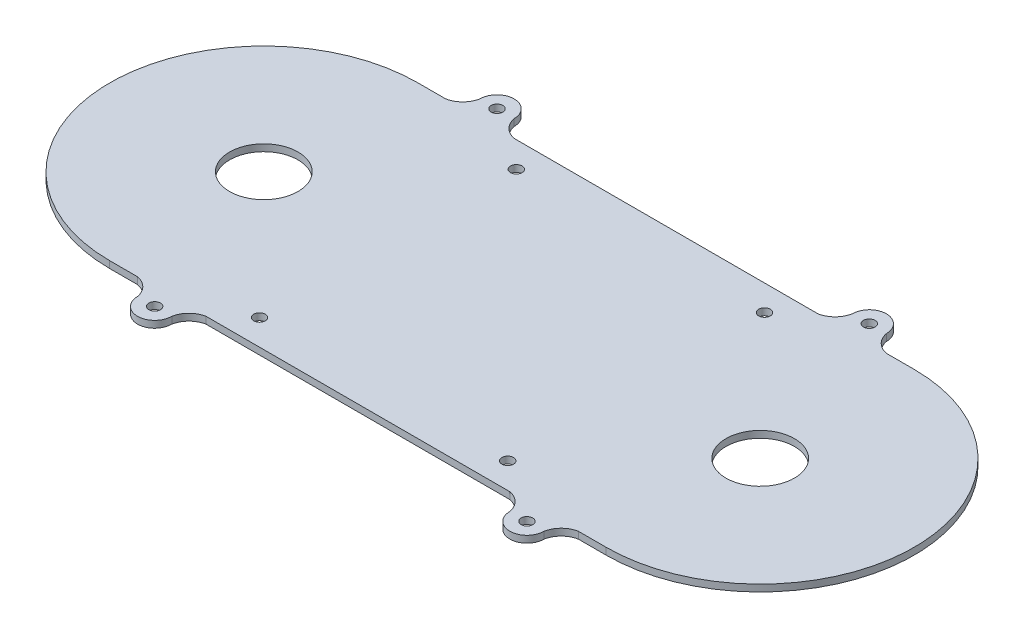
SolidWorks part; units mm, degrees
ref_plane "Front Plane" through (0, 0, 0) normal (0, 0, 1) x (1, 0, 0)
ref_plane "Top Plane" through (0, 0, 0) normal (0, 1, 0) x (1, 0, 0)
ref_plane "Right Plane" through (0, 0, 0) normal (1, 0, 0) x (0, 0, -1)
sketch "Sketch1" plane through (0, 0, 0) normal (0, 1, 0) x (1, 0, 0)
  line L0 (0, 45) -> (8.125, 45)
  line L1 (0, -45) -> (8.125, -45)
  line L2 (0, 0) -> (145, 0) construction
  line L3 (0, -45) -> (8.125, -45)
  line L4 (0, -45) -> (8.125, -45)
  line L6 (145, -45) -> (136.875, -45)
  line L8 (28.125, 45) -> (116.875, 45)
  line L9 (136.875, 45) -> (145, 45)
  line L10 (28.125, -45) -> (116.875, -45)
  line L11 (28.125, -45) -> (36.25, -45)
  line L12 (136.875, -45) -> (145, -45)
  arc A0 (0, 45) -> (0, -45) centre (0, 0) ccw
  arc A1 (145, -45) -> (145, 45) centre (145, 0) ccw
  arc A13 (13.125, -50) -> (23.125, -50) centre (18.125, -50) ccw
  arc A14 (13.125, -50) -> (8.125, -45) centre (6.9406, -51.1844) ccw
  arc A15 (23.125, -50) -> (28.125, -45) centre (29.3094, -51.1844) cw
  arc A16 (121.875, -50) -> (116.875, -45) centre (115.6906, -51.1844) ccw
  arc A17 (121.875, -50) -> (131.875, -50) centre (126.875, -50) ccw
  arc A18 (131.875, -50) -> (136.875, -45) centre (138.0594, -51.1844) cw
  arc A19 (131.875, 50) -> (136.875, 45) centre (138.0594, 51.1844) ccw
  arc A20 (121.875, 50) -> (131.875, 50) centre (126.875, 50) cw
  arc A21 (121.875, 50) -> (116.875, 45) centre (115.6906, 51.1844) cw
  arc A22 (23.125, 50) -> (28.125, 45) centre (29.3094, 51.1844) ccw
  arc A23 (13.125, 50) -> (23.125, 50) centre (18.125, 50) cw
  arc A24 (13.125, 50) -> (8.125, 45) centre (6.9406, 51.1844) cw
  circle A25 centre (108.75, -37.5) radius 1.7
  circle A26 centre (36.25, -37.5) radius 1.7
  circle A27 centre (36.25, 37.5) radius 1.7
  circle A28 centre (108.75, 37.5) radius 1.7
  dimension "D1" = 2
  dimension "D2" = 0
  dimension "D4" = 2
  dimension "D5" = 2
extrude "Boss-Extrude1" add sketch "Sketch1" along normal blind 2
sketch "Sketch2" plane through (0, 2, 0) normal (0, 1, 0) x (1, 0, 0)
  line L0 (0, 0) -> (126.8668, 0) construction
  circle A0 centre (18.1168, -49.9942) radius 5.01
  circle A1 centre (18.1168, -49.9942) radius 1.7
  circle A2 centre (126.8668, -49.9942) radius 1.7
  circle A3 centre (126.8668, 49.9942) radius 1.7
  circle A4 centre (18.1168, 49.9942) radius 1.7
  dimension "D1" = 2
extrude "Cut-Extrude1" cut sketch "Sketch2" against normal blind 4 contours A1 | A2 | A3 | A4
sketch "Sketch3" plane through (0, 0, 0) normal (0, -1, 0) x (-1, 0, 0)
  line L0 (0, 0) -> (-72.5, 0) construction
ref_plane "Plane1" through (72.5, 0, 0) normal (-1, 0, 0) x (0, 0, 1)
sketch "Sketch4" plane through (72.5, 0, 0) normal (-1, 0, 0) x (0, 0, 1)
  line L0 (0, 0) -> (5, 0)
  line L1 (-45, 0) -> (45, 0) construction
  line L2 (0, 0) -> (0, 2)
  line L3 (0, 2) -> (5, 0)
sketch "Sketch5" plane through (0, 2, 0) normal (0, 1, 0) x (1, 0, 0)
  circle A0 centre (0, 0) radius 10
  circle A1 centre (145, 0) radius 10
  dimension "D1" = 2
  dimension "D2" = 20
extrude "Cut-Extrude2" cut sketch "Sketch5" against normal blind 10
sketch "Sketch7" plane through (0, 0, 0) normal (0, -1, 0) x (-1, 0, 0)
  circle A0 centre (-72.5, 0) radius 5
extrude "Boss-Extrude3" add sketch "Sketch7" along normal blind 3
sketch "Sketch9" plane through (72.5, 0, 0) normal (-1, 0, 0) x (0, 0, 1)
  line L0 (0, 0) -> (0, -3)
  line L1 (-5, -3) -> (5, -3) construction
  line L2 (0, -3) -> (-3, -3)
  line L3 (-3, -3) -> (0, 0)
revolve "Cut-Revolve1" cut sketch "Sketch9" angle 360 about L0
